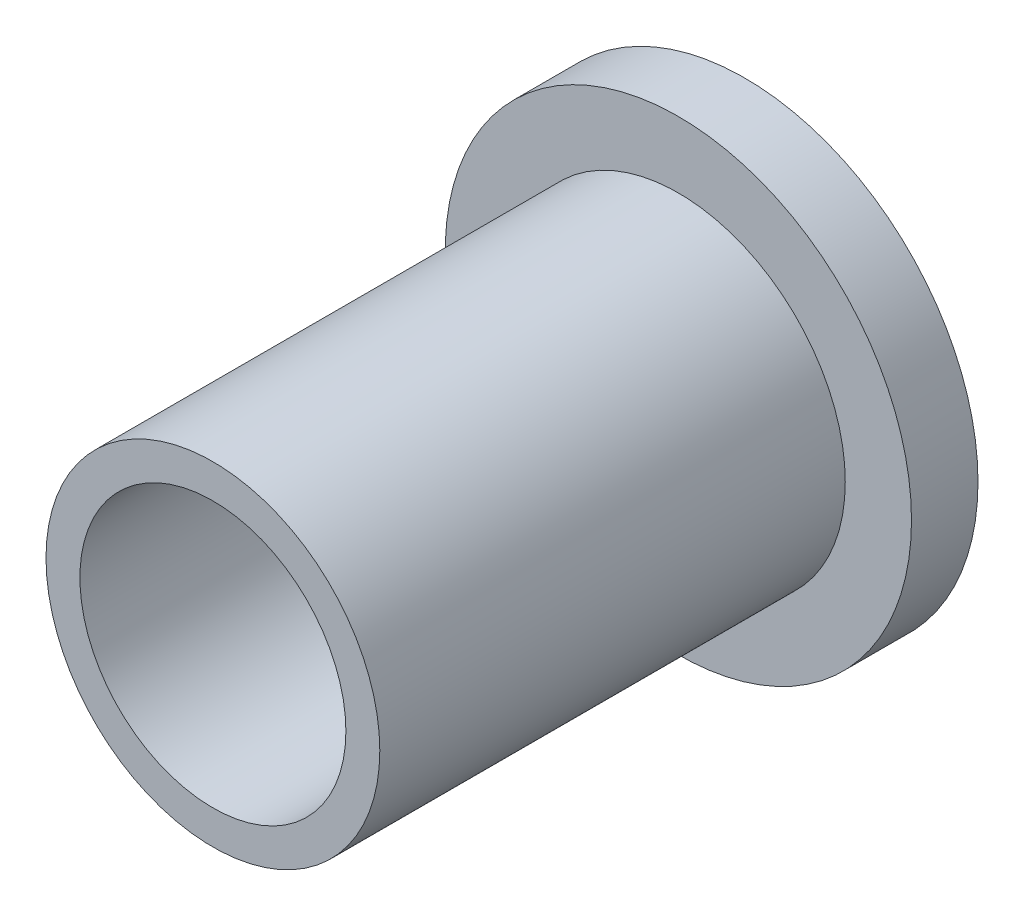
SolidWorks part; units mm, degrees
ref_plane "Front Plane" through (0, 0, 0) normal (0, 0, 1) x (1, 0, 0)
ref_plane "Top Plane" through (0, 0, 0) normal (0, 1, 0) x (1, 0, 0)
ref_plane "Right Plane" through (0, 0, 0) normal (1, 0, 0) x (0, 0, -1)
sketch "Sketch1" plane through (0, 0, 0) normal (0, 0, 1) x (1, 0, 0)
  circle A0 centre (0, 0) radius 6.35
  circle A1 centre (0, 0) radius 11.1315
extrude "Boss-Extrude1" add sketch "Sketch1" along normal blind 3.175
sketch "Sketch2" plane through (0, 0, 3.175) normal (0, 0, 1) x (1, 0, 0)
  circle A0 centre (0, 0) radius 6.35
  circle A1 centre (0, 0) radius 7.9692
extrude "Boss-Extrude2" add sketch "Sketch2" along normal blind 22.225
